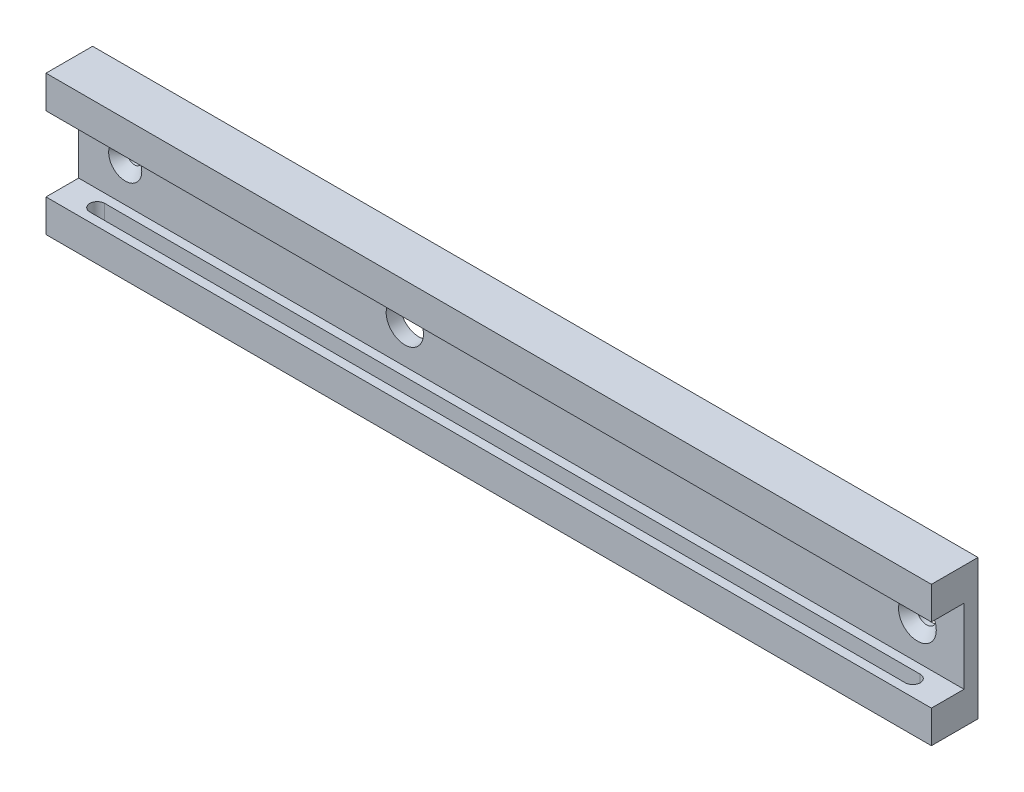
SolidWorks part; units mm, degrees
material "Delrin 2700 NC010, Low Viscosity Acetal Copolymer (SS)"
ref_plane "Front Plane" through (0, 0, 0) normal (0, 0, 1) x (1, 0, 0)
ref_plane "Top Plane" through (0, 0, 0) normal (0, 1, 0) x (1, 0, 0)
ref_plane "Right Plane" through (0, 0, 0) normal (1, 0, 0) x (0, 0, -1)
sketch "Sketch1" plane through (0, 0, 0) normal (0, 0, 1) x (1, 0, 0)
  line L1 (0, 0) -> (190, 0)
  line L2 (0, 0) -> (0, 30)
  line L3 (0, 30) -> (190, 30)
  line L4 (190, 0) -> (190, 30)
  dimension "D1" = 190
  dimension "D2" = 30
extrude "Boss-Extrude1" add sketch "Sketch1" along normal blind 10
sketch "Sketch2" plane through (190, 0, 0) normal (1, 0, 0) x (0, 0, -1)
  line L0 (-10, 0) -> (-10, 30) construction
  line L1 (-10, 7) -> (-3, 7)
  line L2 (-10, 7) -> (-10, 23)
  line L3 (-10, 23) -> (-3, 23)
  line L4 (-3, 7) -> (-3, 23)
  line L5 (0, 15) -> (-10, 15) construction
  line L6 (0, 0) -> (0, 30) construction
  line L7 (-3, 15) -> (-10, 15) construction
  dimension "D1" = 16
  dimension "D2" = 7
extrude "Cut-Extrude1" cut sketch "Sketch2" against normal through all
sketch "Sketch3" plane through (0, 0, 0) normal (0, -1, 0) x (1, 0, 0)
  line L0 (0, 6.5) -> (190, 6.5) construction
  line L1 (0, 10) -> (0, 0) construction
  line L2 (190, 10) -> (190, 0) construction
  line L3 (0, 10) -> (190, 10) construction
  line L4 (7.5, 6.5) -> (182.5, 6.5) construction
  line L5 (7.5, 8.1) -> (182.5, 8.1)
  line L6 (7.5, 4.9) -> (182.5, 4.9)
  line L7 (95, 0) -> (95, 10) construction
  line L8 (0, 0) -> (190, 0) construction
  arc A0 (7.5, 8.1) -> (7.5, 4.9) centre (7.5, 6.5) ccw
  arc A1 (182.5, 4.9) -> (182.5, 8.1) centre (182.5, 6.5) ccw
  point P10 (95, 6.5)
  dimension "D2" = 1.6
  dimension "D1" = 3.5
  dimension "D3" = 175
extrude "Cut-Extrude2" cut sketch "Sketch3" against normal up to next
sketch "Sketch4" plane through (0, 0, 3) normal (0, 0, 1) x (1, 0, 0)
  line L0 (0, 15) -> (190, 15) construction
  line L1 (0, 7) -> (0, 23) construction
  line L2 (190, 7) -> (190, 23) construction
  circle A0 centre (180, 15) radius 2.05
  circle A1 centre (10, 15) radius 1.55
  circle A2 centre (70, 15) radius 4
  dimension "D1" = 4.1
  dimension "D3" = 3.1
  dimension "D6" = 120
  dimension "D5" = 8
  dimension "D2" = 10
  dimension "D4" = 180
extrude "Cut-Extrude3" cut sketch "Sketch4" against normal through all
chamfer "Chamfer1" distance 2 angle 45 1 edges at (182.05, 15, 3)
chamfer "Chamfer2" distance 2 angle 45 1 edges at (11.55, 15, 3)
